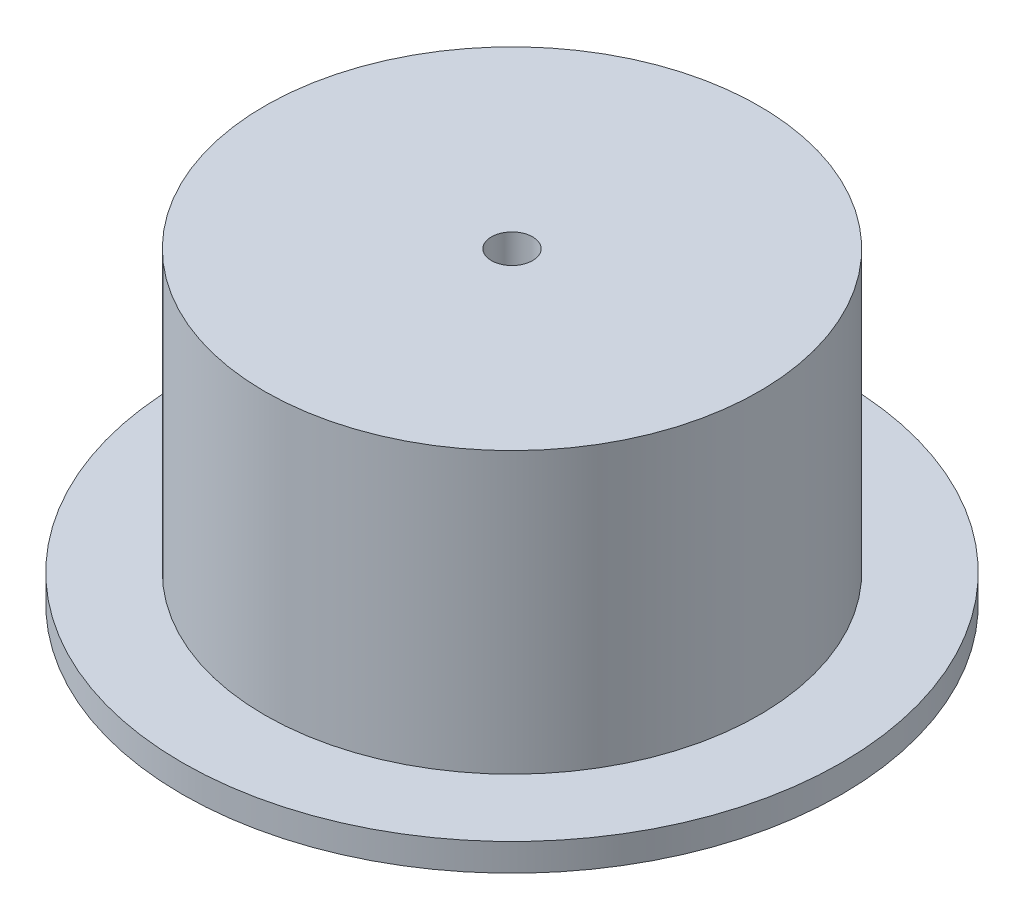
SolidWorks part; units mm, degrees
ref_plane "Front Plane" through (0, 0, 0) normal (0, 0, 1) x (1, 0, 0)
ref_plane "Top Plane" through (0, 0, 0) normal (0, 1, 0) x (1, 0, 0)
ref_plane "Right Plane" through (0, 0, 0) normal (1, 0, 0) x (0, 0, -1)
sketch "Sketch1" plane through (0, 0, 0) normal (0, 1, 0) x (1, 0, 0)
  circle A0 centre (0, 0) radius 60
  circle A1 centre (0, 0) radius 45
  dimension "D1" = 120
extrude "Boss-Extrude1" add sketch "Sketch1" along normal blind 5
sketch "Sketch2" plane through (0, 0, 0) normal (0, 1, 0) x (1, 0, 0)
  circle A0 centre (0, 0) radius 45
  circle A1 centre (0, 0) radius 40
extrude "Boss-Extrude2" add sketch "Sketch2" along normal blind 56
sketch "Sketch3" plane through (0, 56, 0) normal (0, 1, 0) x (1, 0, 0)
  circle A0 centre (0, 0) radius 3.75
  circle A1 centre (0, 0) radius 40
extrude "Boss-Extrude3" add sketch "Sketch3" against normal blind 10
